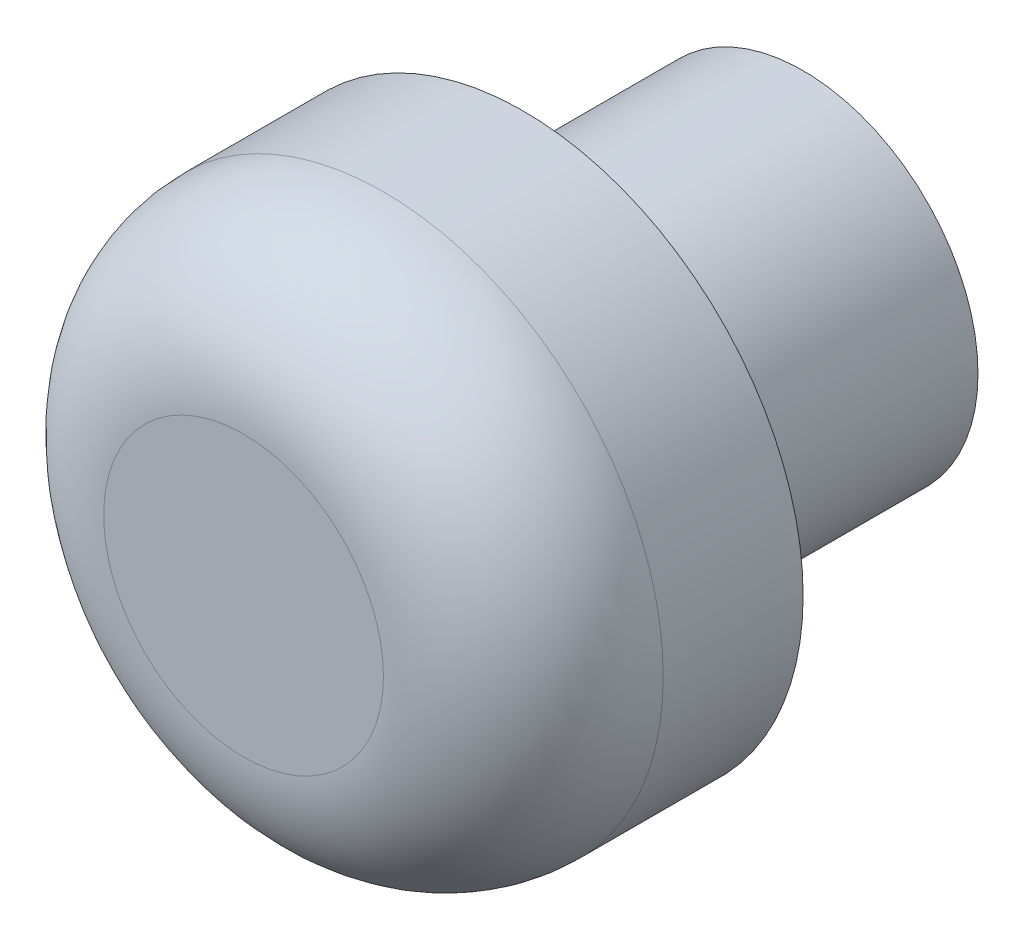
SolidWorks part; units mm, degrees
material "AISI 1020"
ref_plane "Plano frontal" through (0, 0, 0) normal (0, 0, 1) x (1, 0, 0)
ref_plane "Plano superior" through (0, 0, 0) normal (0, 1, 0) x (1, 0, 0)
ref_plane "Plano direito" through (0, 0, 0) normal (1, 0, 0) x (0, 0, -1)
sketch "Esboço1" plane through (0, 0, 0) normal (0, 0, 1) x (1, 0, 0)
  circle A0 centre (0, 0) radius 20
  dimension "D1" = 40
extrude "Ressalto-extrusão1" add sketch "Esboço1" along normal blind 20
fillet "Filete1" radius 10 1 edges at (20, 0, 20)
sketch "Esboço3" plane through (0, 0, 0) normal (0, 0, -1) x (-1, 0, 0)
  circle A0 centre (0, 0) radius 12.5
  dimension "D1" = 25
extrude "Ressalto-extrusão2" add sketch "Esboço3" along normal blind 20
sketch "Esboço6" plane through (0, 0, -20) normal (0, 0, -1) x (-1, 0, 0)
  circle A0 centre (0, 0) radius 3
  dimension "D1" = 6
extrude "Corte-extrusão1" cut sketch "Esboço6" against normal blind 30
cosmetic thread "Representação de rosca1" parameters "D2"=7
thread "Rosca1" pitch 1 start angle 0, offset 0, length 10, pitch 1, diameter 6
ref_plane "Plano1" through (3, 0, -20) normal (0, -1, 0) x (1, 0, 0)
sketch "Perfil da rosca1" plane through (3, 0, -20) normal (0, -1, 0) x (1, 0, 0)
  line L0 (0, 0) -> (0, 1) construction
  line L11 (0, 0) -> (0, 0.875)
  line L12 (0, 0.875) -> (-0.5413, 0.5625)
  line L13 (-0.5413, 0.5625) -> (-0.5413, 0.3125)
  line L15 (-0.5413, 0.3125) -> (0, 0)
  line L17 (-0.5413, 0.4375) -> (0, 0.4375) construction
  point P2 (0, 0)
  dimension "Pitch" = 1
  dimension "Profile_Angle" = 60
  dimension "Profile_Land" = 0.25
  dimension "Profile_Height" = 0.5413
